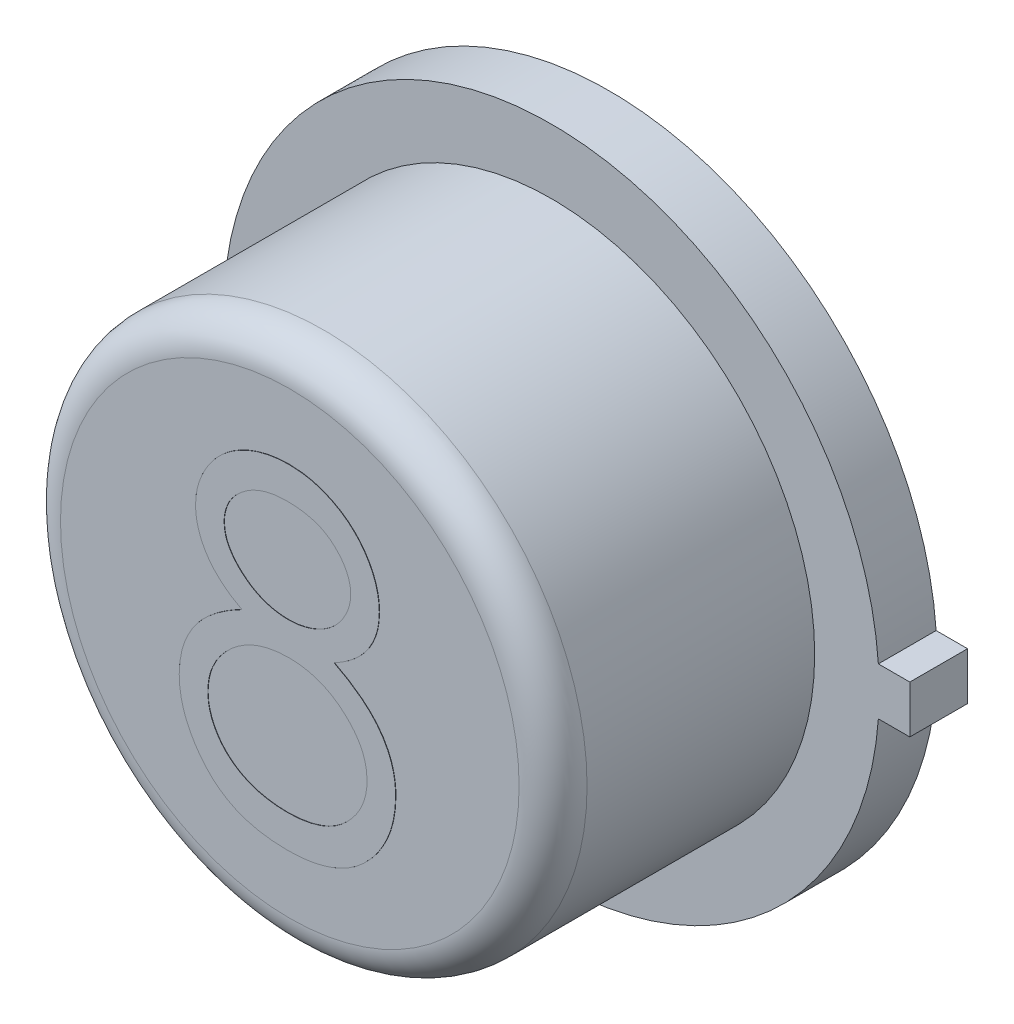
SolidWorks part; units mm, degrees
ref_plane "Front Plane" through (0, 0, 0) normal (0, 0, 1) x (1, 0, 0)
ref_plane "Top Plane" through (0, 0, 0) normal (0, 1, 0) x (1, 0, 0)
ref_plane "Right Plane" through (0, 0, 0) normal (1, 0, 0) x (0, 0, -1)
sketch "Sketch1" plane through (0, 0, 0) normal (0, 0, 1) x (1, 0, 0)
  line L1 (2.4511, 0.1778) -> (2.6797, 0.1778)
  line L3 (2.4511, -0.1778) -> (2.6797, -0.1778)
  line L4 (2.6797, 0.1778) -> (2.6797, -0.1778)
  line L5 (2.4511, 0.1778) -> (2.4444, 0.1778)
  line L6 (2.4511, -0.1778) -> (2.4446, -0.1778)
  arc A0 (2.4446, 0.1778) -> (2.4446, -0.1778) centre (0, 0) ccw
  dimension "D1" = 4.9022
  dimension "D2" = 0.3556
  dimension "D3" = 0.2286
extrude "Boss-Extrude1" add sketch "Sketch1" along normal blind 0.4318
sketch "Sketch2" plane through (0, 0, 0.4318) normal (0, 0, 1) x (1, 0, 0)
  circle A0 centre (0, 0) radius 1.9685
  dimension "D1" = 3.937
extrude "Boss-Extrude2" add sketch "Sketch2" along normal blind 1.9558
sketch "Sketch3" plane through (0, 0, 0) normal (0, 0, -1) x (-1, 0, 0)
  circle A0 centre (0, 0) radius 1.7576
extrude "Boss-Extrude3" add sketch "Sketch3" along normal blind 0.0025
fillet "Fillet1" radius 0.254 1 edges at (1.9685, 0, 2.3876)
sketch "Sketch4" plane through (0, 0, 2.3876) normal (0, 0, 1) x (1, 0, 0)
  line L0 (-1.2065, -1.2181) -> (1.2065, -1.2181) construction
  circle A0 centre (0, 0) radius 1.7145 construction
  text T0 "8" font "Century Gothic" height in points 9
  dimension "D1" = 2.413
extrude "Boss-Extrude6" add sketch "Sketch4" along normal blind 0.0025
